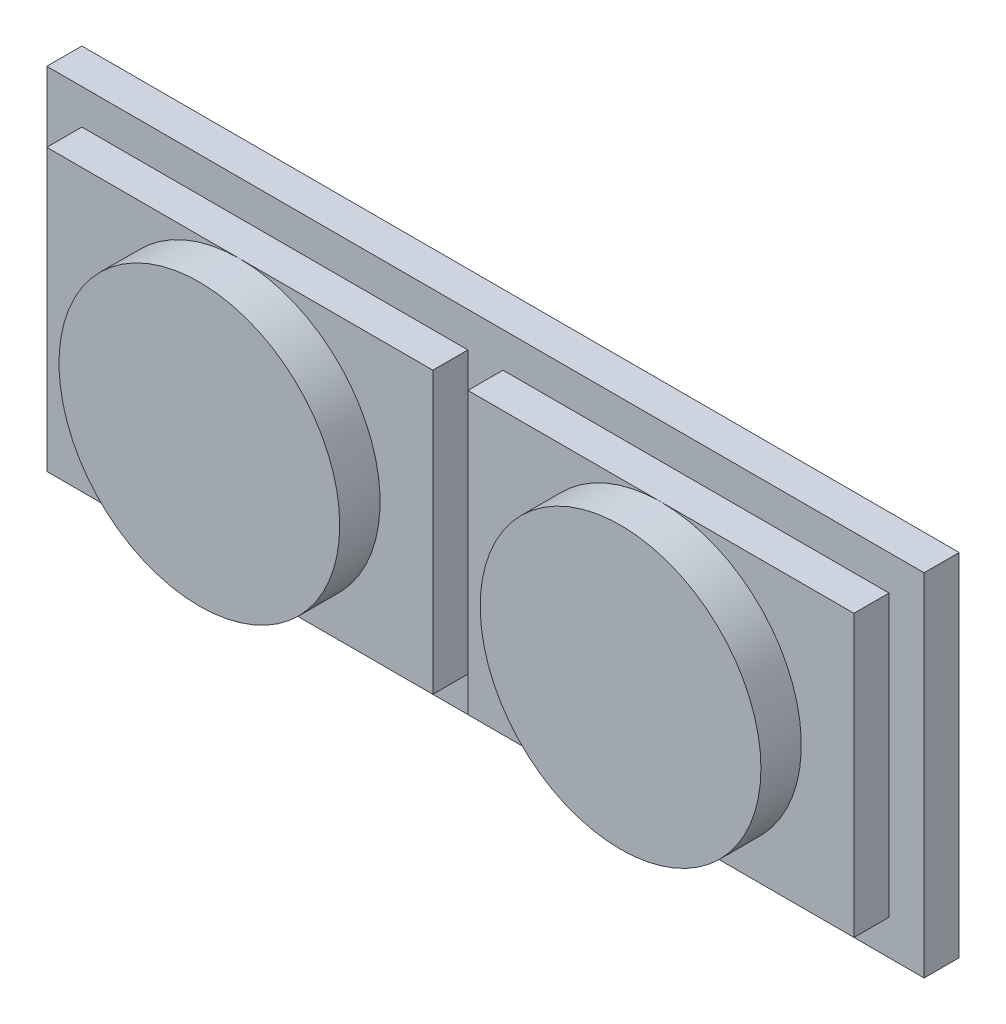
SolidWorks part; units mm, degrees
ref_plane "Front Plane" through (0, 0, 0) normal (0, 0, 1) x (1, 0, 0)
ref_plane "Top Plane" through (0, 0, 0) normal (0, 1, 0) x (1, 0, 0)
ref_plane "Right Plane" through (0, 0, 0) normal (1, 0, 0) x (0, 0, -1)
sketch "Sketch1" plane through (0, 0, 0) normal (0, 0, 1) x (1, 0, 0)
  line L1 (0, 0) -> (6.35, 0)
  line L2 (0, 0) -> (0, 2.54)
  line L3 (0, 2.54) -> (6.35, 2.54)
  line L4 (6.35, 0) -> (6.35, 2.54)
  dimension "D1" = 6.35
  dimension "D2" = 2.54
extrude "Boss-Extrude1" add sketch "Sketch1" along normal blind 0.254
sketch "Sketch2" plane through (0, 0, 0.254) normal (0, 0, 1) x (1, 0, 0)
  line L0 (6.35, 0) -> (6.35, 2.54) construction
  line L2 (0.254, 0.254) -> (0.254, 2.286)
  line L4 (6.096, 0.254) -> (6.096, 2.286)
  line L6 (0.254, 2.286) -> (3.048, 2.286)
  line L7 (6.096, 2.286) -> (3.302, 2.286)
  line L8 (0.254, 0.254) -> (3.048, 0.254)
  line L9 (3.302, 0.254) -> (6.096, 0.254)
  line L10 (3.302, 0.254) -> (3.302, 2.286)
  line L11 (3.048, 2.286) -> (3.048, 0.254)
  dimension "D1" = 5.842
  dimension "D2" = 0.254
  dimension "D3" = 2.032
  dimension "D4" = 2.794
  dimension "D5" = 2.794
  dimension "D6" = 2.032
extrude "Boss-Extrude3" add sketch "Sketch2" along normal blind 0.254 separate body contours L6 L11 L8 L2 | L10 L7 L4 L9
sketch "Sketch4" plane through (0, 0, 0.508) normal (0, 0, 1) x (1, 0, 0)
  line L0 (0.254, 2.286) -> (3.0468, 0.254) construction
  line L1 (0.254, 2.286) -> (3.048, 2.286) construction
  line L2 (0.254, 0.254) -> (3.048, 0.254) construction
  line L3 (0.254, 0.254) -> (3.048, 2.286) construction
  circle A0 centre (1.6504, 1.27) radius 1.016
  dimension "D1" = 2.032
extrude "Boss-Extrude4" add sketch "Sketch4" along normal blind 0.2921
sketch "Sketch5" plane through (0, 0, 0.508) normal (0, 0, 1) x (1, 0, 0)
  line L0 (3.302, 2.286) -> (6.096, 0.254) construction
  line L1 (3.302, 0.254) -> (6.096, 2.286) construction
  circle A0 centre (4.699, 1.27) radius 1.016
  dimension "D1" = 2.032
extrude "Boss-Extrude5" add sketch "Sketch5" along normal blind 0.2921
